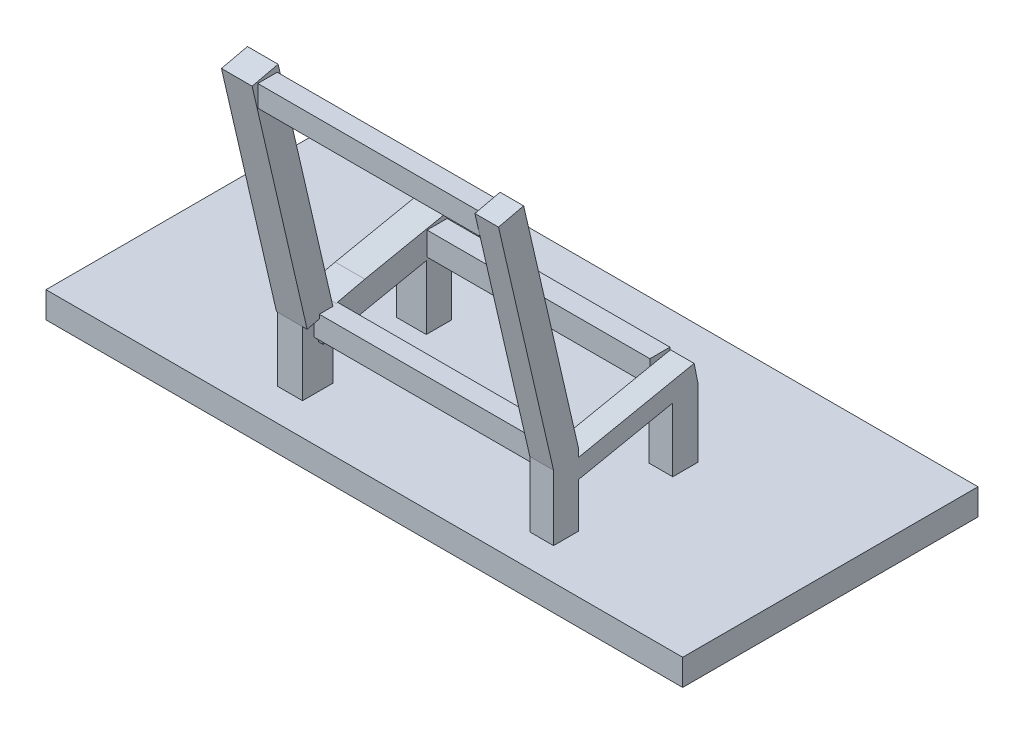
SolidWorks part; units mm, degrees
ref_plane "Front Plane" through (0, 0, 0) normal (0, 0, 1) x (1, 0, 0)
ref_plane "Top Plane" through (0, 0, 0) normal (0, 1, 0) x (1, 0, 0)
ref_plane "Right Plane" through (0, 0, 0) normal (1, 0, 0) x (0, 0, -1)
sketch "Sketch1" plane through (0, 0, 0) normal (0, 1, 0) x (1, 0, 0)
  line L1 (-35.8969, 26.15) -> (37.0682, 26.15)
  line L2 (-35.8969, 26.15) -> (-35.8969, -7.6941)
  line L3 (-35.8969, -7.6941) -> (37.0682, -7.6941)
  line L4 (37.0682, 26.15) -> (37.0682, -7.6941)
  point P4 (41.1225, -11.9182)
extrude "Boss-Extrude1" add sketch "Sketch1" along normal blind 3
sketch "Sketch2" plane through (0, 0, 7.6941) normal (0, 0, 1) x (1, 0, 0)
  circle A0 centre (-27.6974, -3.0249) radius 3.3322
  circle A1 centre (35.7739, -4.0888) radius 3.1715
  point P4 (-27.6974, -3.0249)
extrude "Boss-Extrude2" [suppressed] add sketch "Sketch2" against normal up to vertex separate body
sketch "Sketch3" plane through (0, 3, 0) normal (0, 1, 0) x (1, 0, 0)
  line L1 (-13.0563, -0.501) -> (-10.1741, -0.501)
  line L2 (-13.0563, -0.501) -> (-13.0563, -4.0172)
  line L3 (-13.0563, -4.0172) -> (-10.1741, -4.0172)
  line L4 (-10.1741, -0.501) -> (-10.1741, -4.0172)
  line L5 (15.8802, -1.1351) -> (18.5894, -1.1351)
  line L6 (15.8802, -1.1351) -> (15.8802, -4.0172)
  line L7 (15.8802, -4.0172) -> (18.5894, -4.0172)
  line L8 (18.5894, -1.1351) -> (18.5894, -4.0172)
  line L9 (-13.0563, 12.5262) -> (-9.6554, 12.5262)
  line L10 (-13.0563, 12.5262) -> (-13.0563, 9.644)
  line L11 (-13.0563, 9.644) -> (-9.6554, 9.644)
  line L12 (-9.6554, 12.5262) -> (-9.6554, 9.644)
  line L13 (15.8802, 12.5262) -> (18.5894, 12.5262)
  line L14 (15.8802, 12.5262) -> (15.8802, 9.644)
  line L15 (15.8802, 9.644) -> (18.5894, 9.644)
  line L16 (18.5894, 12.5262) -> (18.5894, 9.644)
extrude "Boss-Extrude3" add sketch "Sketch3" along normal blind 20
sketch "Sketch5" plane through (18.5894, 0, 0) normal (1, 0, 0) x (0, 0, -1)
  line L0 (-4.0172, 23) -> (12.5262, 20.9687)
  line L1 (12.5262, 23) -> (12.5262, 3) construction
  line L2 (12.5262, 20.9687) -> (12.5262, 23)
  line L3 (12.5262, 23) -> (-4.0172, 23)
  line L4 (9.644, 23) -> (12.5262, 23) construction
  point P6 (0, 0)
  dimension "D1" = 7
extrude "Cut-Extrude1" cut sketch "Sketch5" against normal through all
sketch "Sketch6" plane through (18.5894, 0, 0) normal (1, 0, 0) x (0, 0, -1)
  line L0 (9.644, 10.3293) -> (12.5262, 10.9171)
  line L1 (9.644, 21.3226) -> (9.644, 3) construction
  line L2 (12.5262, 20.9687) -> (12.5262, 3) construction
  line L3 (12.5262, 10.9171) -> (13.8517, 22.4565)
  line L4 (13.8517, 22.4565) -> (7.6025, 22.7968)
  line L5 (7.6025, 22.7968) -> (9.644, 10.3293)
  point P8 (12.5262, 10.9171)
extrude "Cut-Extrude3" cut sketch "Sketch6" against normal through all
ref_plane "Plane2" through (0, 2.8886, -14.1635) normal (0, -0.1998, 0.9798) x (1, 0, 0)
sketch "Sketch7" plane through (0, 2.8886, -14.1635) normal (0, -0.1998, 0.9798) x (1, 0, 0)
  line L0 (-13.0563, 23.3389) -> (-13.0563, 3.7423) construction
  line L1 (-9.6554, 8.1938) -> (-13.0563, 8.1938)
  line L2 (-9.6554, 8.1938) -> (-9.6554, 11.2533)
  line L3 (-9.6554, 11.2533) -> (-13.0563, 11.2533)
  line L4 (-13.0563, 8.1938) -> (-13.0563, 11.2533)
  line L5 (15.8802, 23.3389) -> (15.8802, 3.7423) construction
  line L6 (15.8802, 8.1938) -> (18.5894, 8.1938)
  line L7 (15.8802, 8.1938) -> (15.8802, 10.3487)
  line L8 (15.8802, 10.3487) -> (18.5894, 10.3487)
  line L9 (18.5894, 8.1938) -> (18.5894, 10.3487)
  line L10 (18.5894, 23.3389) -> (18.5894, 3.7423) construction
extrude "Boss-Extrude4" add sketch "Sketch7" along normal blind 15
sketch "Sketch9" plane through (-13.0563, 0, 0) normal (-1, 0, 0) x (0, 0, 1)
  line L0 (-2.6069, 12.0166) -> (17.0707, 7.4698)
  line L1 (0.501, 11.3828) -> (-11.9148, 13.9149) construction
  line L2 (17.0707, 7.4698) -> (5.0325, 29.0007)
  line L3 (5.0325, 29.0007) -> (-3.8768, 23.4854)
  line L4 (-3.8768, 23.4854) -> (-2.6069, 12.0166)
extrude "Cut-Extrude4" cut sketch "Sketch9" against normal through all
sketch "Sketch10" plane through (0, 10.8357, 2.5037) normal (0, 0.9743, 0.2251) x (1, 0, 0)
  line L0 (-13.0563, 5.2453) -> (-13.0563, -1.5533) construction
  line L1 (-13.0563, 1.3931) -> (-9.5401, 1.3931)
  line L2 (-13.0563, 1.3931) -> (-13.0563, -1.662)
  line L3 (-13.0563, -1.662) -> (-9.5401, -1.662)
  line L4 (-9.5401, 1.3931) -> (-9.5401, -1.662)
  line L5 (18.5894, -3.2387) -> (18.5894, -0.4305) construction
  line L6 (15.8802, 1.4047) -> (18.5894, 1.4047)
  line L7 (15.8802, 1.4047) -> (15.8802, -1.5533)
  line L8 (15.8802, -1.5533) -> (18.5894, -1.5533)
  line L9 (18.5894, 1.4047) -> (18.5894, -1.5533)
  line L10 (18.5894, 1.4047) -> (18.5894, -1.5533) construction
extrude "Boss-Extrude6" add sketch "Sketch10" along normal blind 28
sketch "Sketch8" plane through (15.8802, 0, 0) normal (-1, 0, 0) x (0, 0, 1)
  line L0 (-14.4613, 1.4286) -> (-13.8658, 4.3486) construction
  line L1 (-12.0362, 13.3195) -> (-9.7371, 13.3195)
  line L2 (-12.0362, 13.3195) -> (-12.0362, 10.6387)
  line L3 (-12.0362, 10.6387) -> (-9.7371, 10.6387)
  line L4 (-9.7371, 13.3195) -> (-9.7371, 10.6387)
  line L6 (0.5029, 11.2574) -> (2.7303, 11.2574)
  line L7 (0.5029, 11.2574) -> (0.5029, 8.6897)
  line L8 (0.5029, 8.6897) -> (2.7303, 8.6897)
  line L9 (2.7303, 11.2574) -> (2.7303, 8.6897)
  line L10 (7.5537, 37.6855) -> (9.7811, 37.6855)
  line L11 (7.5537, 37.6855) -> (7.5537, 35.2415)
  line L12 (7.5537, 35.2415) -> (9.7811, 35.2415)
  line L13 (9.7811, 37.6855) -> (9.7811, 35.2415)
extrude "Boss-Extrude5" add sketch "Sketch8" along normal blind 28
scale "Scale1" bodies to scale 109 103 102 scale about centroid uniform scaling yes scale factor 20
